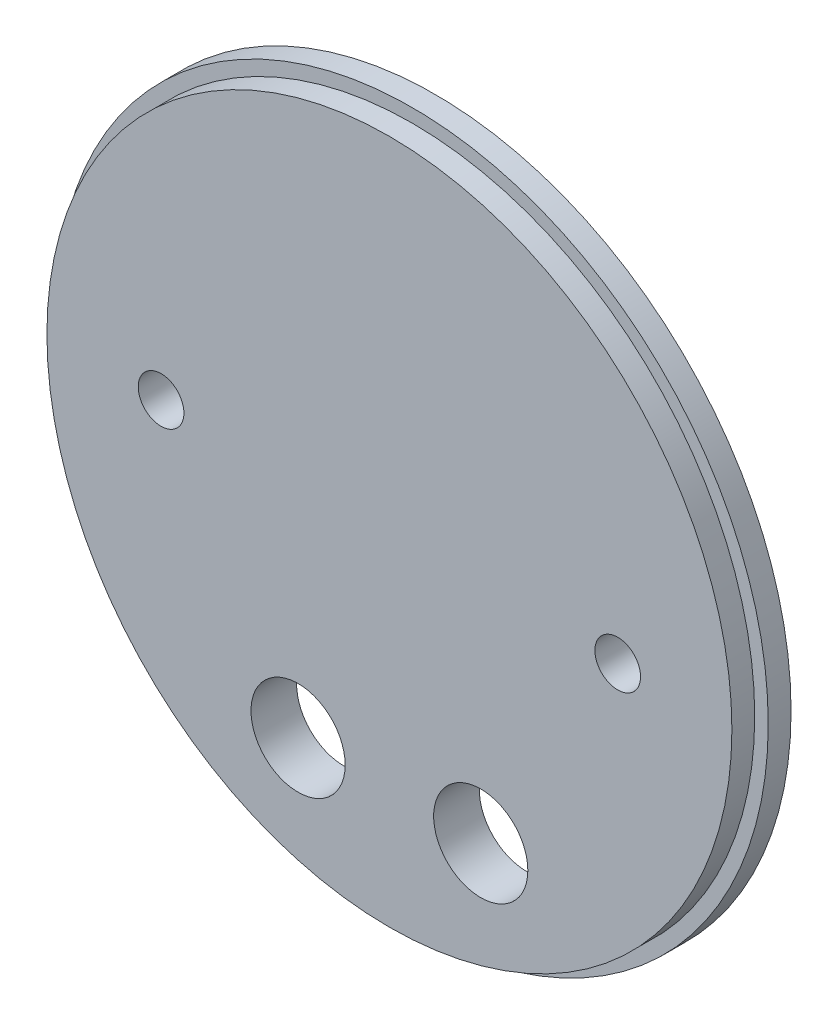
SolidWorks part; units mm, degrees
ref_plane "Front Plane" through (0, 0, 0) normal (0, 0, 1) x (1, 0, 0)
ref_plane "Top Plane" through (0, 0, 0) normal (0, 1, 0) x (1, 0, 0)
ref_plane "Right Plane" through (0, 0, 0) normal (1, 0, 0) x (0, 0, -1)
sketch "Sketch1" plane through (0, 0, 0) normal (0, 0, 1) x (1, 0, 0)
  circle A0 centre (0, 0) radius 49.5046
  dimension "D1" = 99.0092
extrude "Boss-Extrude1" add sketch "Sketch1" along normal blind 3.175
sketch "Sketch2" plane through (0, 0, 3.175) normal (0, 0, 1) x (1, 0, 0)
  circle A0 centre (0, 0) radius 47.625
  dimension "D1" = 95.25
extrude "Boss-Extrude2" add sketch "Sketch2" along normal blind 3.175
sketch "Sketch3" plane through (0, 0, 6.35) normal (0, 0, 1) x (1, 0, 0)
  circle A0 centre (-12.7, -31.1668) radius 6.5484
  circle A1 centre (-12.7, -31.1668) radius 12.7 construction
  circle A2 centre (-12.7, -31.1668) radius 13.97 construction
  circle A3 centre (12.7, -31.1668) radius 6.5484
  circle A4 centre (12.7, -31.1668) radius 12.7 construction
  circle A5 centre (12.7, -31.1668) radius 13.97 construction
  circle A6 centre (0, 0) radius 47.625 construction
  circle A7 centre (-31.75, 0) radius 3.175
  circle A8 centre (31.75, 0) radius 3.175
  dimension "D1" = 13.0969
  dimension "D2" = 25.4
  dimension "D3" = 27.94
  dimension "D4" = 63.5
  dimension "D6" = 6.35
  dimension "D5" = 31.75
extrude "Cut-Extrude1" cut sketch "Sketch3" against normal through all
